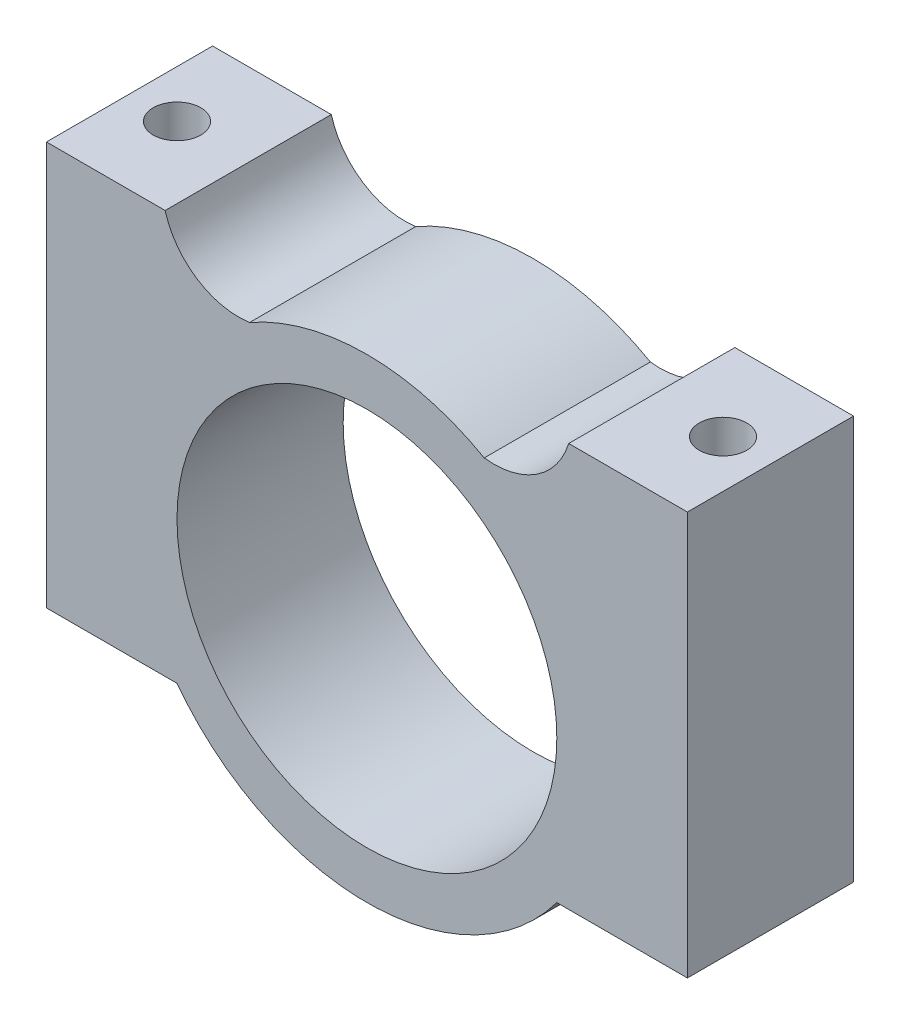
SolidWorks part; units mm, degrees
ref_plane "Front Plane" through (0, 0, 0) normal (0, 0, 1) x (1, 0, 0)
ref_plane "Top Plane" through (0, 0, 0) normal (0, 1, 0) x (1, 0, 0)
ref_plane "Right Plane" through (0, 0, 0) normal (1, 0, 0) x (0, 0, -1)
sketch "Sketch1" plane through (0, 0, 0) normal (0, 0, 1) x (1, 0, 0)
  line L0 (0, 0) -> (0, -2.5) construction
  line L1 (-13.5, 8.5) -> (-8.5, 8.5)
  line L2 (-13.5, 8.5) -> (-13.5, -8.5)
  line L3 (-13.5, -8.5) -> (-8, -8.5)
  line L4 (13.5, 8.5) -> (13.5, -8.5)
  line L5 (-13.5, 8.5) -> (13.5, -8.5) construction
  line L6 (-13.5, -8.5) -> (13.5, 8.5) construction
  line L7 (8, -8.5) -> (13.5, -8.5)
  line L8 (8.5, 8.5) -> (13.5, 8.5)
  line L9 (-4.9411, 6.194) -> (4.9411, 6.194) construction
  circle A0 centre (0, -2.5) radius 8
  arc A1 (-8, -8.5) -> (8, -8.5) centre (0, -2.5) ccw
  arc A2 (-8.5, 8.5) -> (-4.9411, 6.194) centre (-5.4098, 9.37) ccw
  arc A3 (8.5, 8.5) -> (4.9411, 6.194) centre (5.3523, 9.4587) cw
  arc A4 (4.9411, 6.194) -> (-4.9411, 6.194) centre (0, -2.5) ccw
  point P0 (0, 0)
  dimension "D1" = 27
  dimension "D3" = 16
  dimension "D6" = 16
  dimension "D2" = 17
  dimension "D4" = 5
  dimension "D5" = 5
  dimension "D7" = 2.5
extrude "Boss-Extrude1" add sketch "Sketch1" along normal blind 7
sketch "Sketch2" plane through (0, 8.5, 0) normal (0, 1, 0) x (1, 0, 0)
  line L0 (-11.5, -3.5) -> (11.5, -3.5) construction
  circle A0 centre (-11.5, -3.5) radius 1
  circle A1 centre (11.5, -3.5) radius 1
  dimension "D1" = 2
  dimension "D2" = 2
  dimension "D3" = 11.5
  dimension "D4" = 11.5
extrude "Cut-Extrude1" cut sketch "Sketch2" against normal through all
